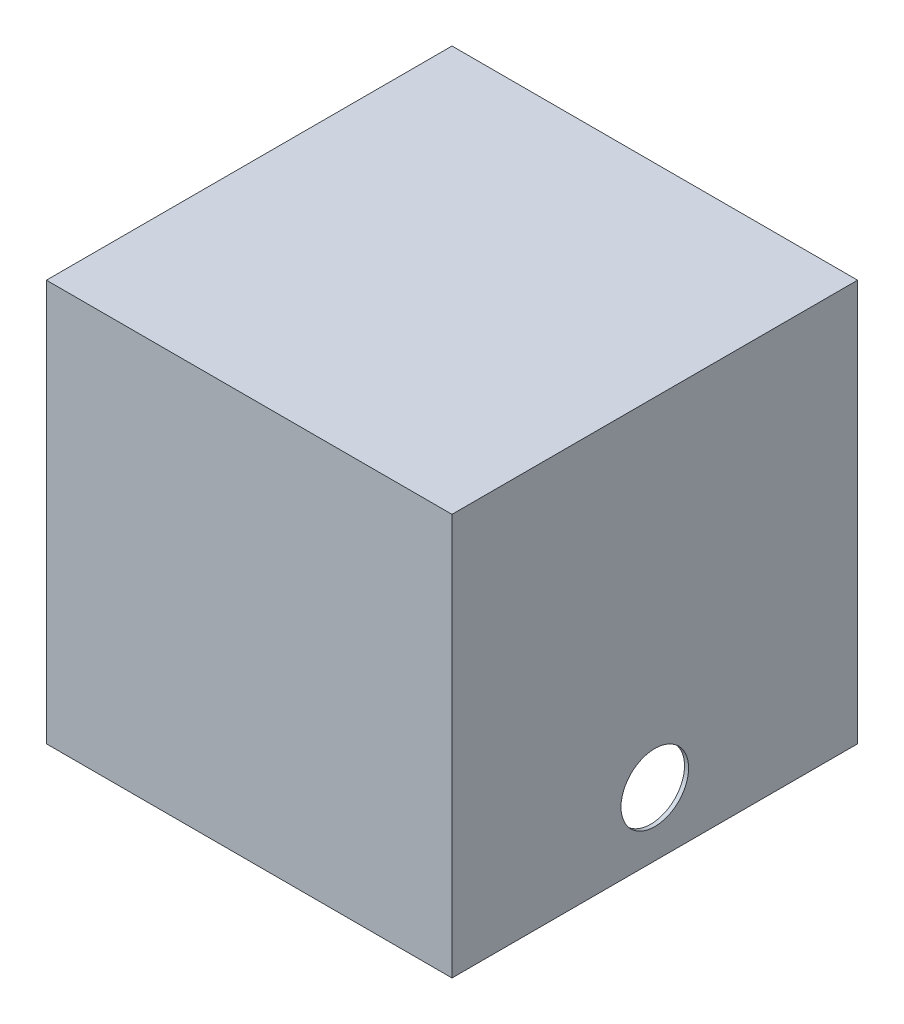
SolidWorks part; units mm, degrees
material "Acrylic (Medium-high impact)"
ref_plane "Front Plane" through (0, 0, 0) normal (0, 0, 1) x (1, 0, 0)
ref_plane "Top Plane" through (0, 0, 0) normal (0, 1, 0) x (1, 0, 0)
ref_plane "Right Plane" through (0, 0, 0) normal (1, 0, 0) x (0, 0, -1)
sketch "Sketch1" plane through (0, 0, 0) normal (0, 1, 0) x (1, 0, 0)
  line L1 (150, 150) -> (-150, 150)
  line L2 (150, 150) -> (150, -150)
  line L3 (150, -150) -> (-150, -150)
  line L4 (-150, 150) -> (-150, -150)
  line L5 (150, 150) -> (-150, -150) construction
  line L6 (150, -150) -> (-150, 150) construction
  point P0 (0, 0)
  dimension "D1" = 300
  dimension "D2" = 300
extrude "Boss-Extrude1" add sketch "Sketch1" along normal blind 3
sketch "Sketch2" plane through (0, 3, 0) normal (0, 1, 0) x (1, 0, 0)
  line L1 (150, 150) -> (-150, 150)
  line L2 (150, 150) -> (150, -150)
  line L3 (150, -150) -> (-150, -150)
  line L4 (-150, 150) -> (-150, -150)
  line L5 (150, 150) -> (-150, -150) construction
  line L6 (150, -150) -> (-150, 150) construction
  line L7 (147, 147) -> (-147, 147)
  line L8 (147, 147) -> (147, -147)
  line L9 (147, -147) -> (-147, -147)
  line L10 (-147, 147) -> (-147, -147)
  line L11 (147, 147) -> (-147, -147) construction
  line L12 (147, -147) -> (-147, 147) construction
  point P0 (0, 0)
  point P7 (0, 0)
  dimension "D1" = 294
extrude "Boss-Extrude2" add sketch "Sketch2" along normal blind 297
sketch "Sketch3" plane through (0, 300, 0) normal (0, 1, 0) x (1, 0, 0)
  line L1 (150, 150) -> (-150, 150)
  line L2 (150, 150) -> (150, -150)
  line L3 (150, -150) -> (-150, -150)
  line L4 (-150, 150) -> (-150, -150)
  line L5 (150, 150) -> (-150, -150) construction
  line L6 (150, -150) -> (-150, 150) construction
  point P0 (0, 0)
extrude "Boss-Extrude3" add sketch "Sketch3" against normal blind 3
sketch "Sketch4" plane through (150, 0, 0) normal (1, 0, 0) x (0, 0, -1)
  circle A0 centre (0, 50) radius 25
  dimension "D1" = 50
  dimension "D2" = 50
extrude "Cut-Extrude1" cut sketch "Sketch4" against normal through all both and the other way through all
sketch "Sketch5" plane through (0, 0, 0) normal (0, -1, 0) x (1, 0, 0)
  line L1 (150, 150) -> (-150, 150)
  line L2 (150, 150) -> (150, -150)
  line L3 (150, -150) -> (-150, -150)
  line L4 (-150, 150) -> (-150, -150)
  line L5 (150, 150) -> (-150, -150) construction
  line L6 (150, -150) -> (-150, 150) construction
  point P0 (0, 0)
extrude "Cut-Extrude2" cut sketch "Sketch5" against normal blind 3
